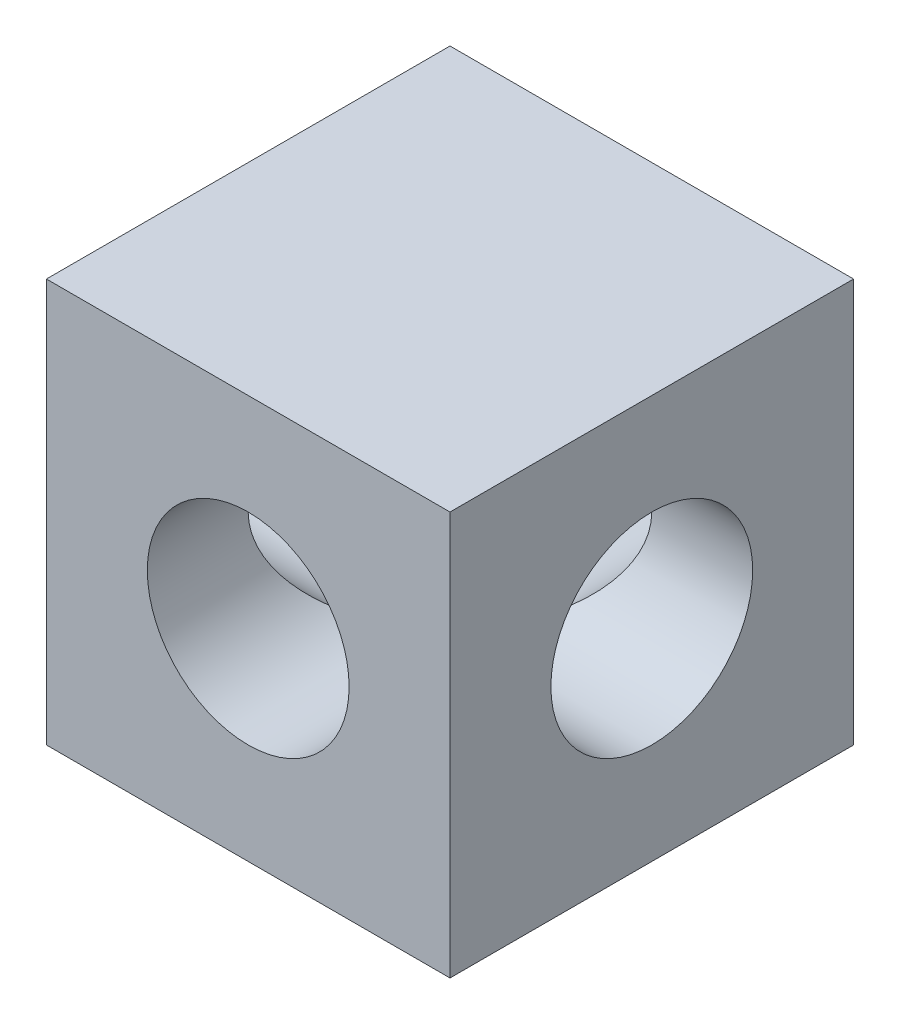
SolidWorks part; units mm, degrees
ref_plane "Front" through (0, 0, 0) normal (0, 0, 1) x (1, 0, 0)
ref_plane "Top" through (0, 0, 0) normal (0, 1, 0) x (-1, 0, 0)
ref_plane "Right" through (0, 0, 0) normal (1, 0, 0) x (0, 0, -1)
sketch "Sketch1" plane through (0, 0, 0) normal (0, 0, 1) x (1, 0, 0)
  line L0 (-9.525, -9.525) -> (9.525, -9.525)
  line L1 (-9.525, -9.525) -> (-9.525, 9.525)
  line L2 (9.525, 9.525) -> (-9.525, 9.525)
  line L3 (9.525, 9.525) -> (9.525, -9.525)
  line L4 (9.525, 9.525) -> (-9.525, -9.525) construction
  circle A0 centre (0, 0) radius 4.7625
extrude "Base-Extrude" add sketch "Sketch1" along normal mid plane 19.05
sketch "Sketch3" plane through (9.525, 0, 0) normal (1, 0, 0) x (0, 0, -1)
  circle A0 centre (0, 0) radius 4.7625
extrude "Cut-Extrude1" cut sketch "Sketch3" against normal through all
scale "Scale1" scale about centroid uniform scaling yes scale factor 0.8
